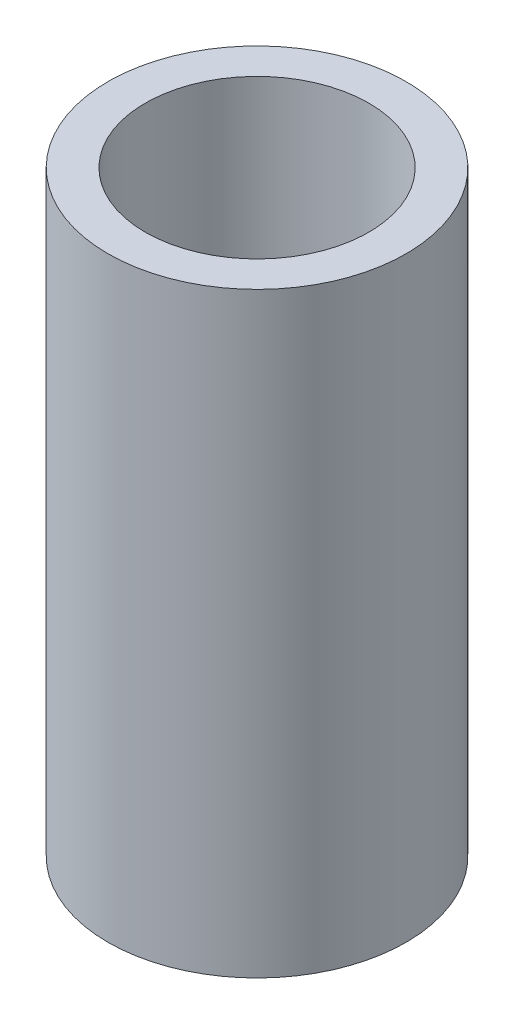
SolidWorks part; units mm, degrees
ref_plane "Front Plane" through (0, 0, 0) normal (0, 0, 1) x (1, 0, 0)
ref_plane "Top Plane" through (0, 0, 0) normal (0, 1, 0) x (1, 0, 0)
ref_plane "Right Plane" through (0, 0, 0) normal (1, 0, 0) x (0, 0, -1)
sketch "Sketch1" plane through (0, 0, 0) normal (0, 1, 0) x (1, 0, 0)
  circle A0 centre (0, 0) radius 1.5
  circle A1 centre (0, 0) radius 2
  dimension "D1" = 3
  dimension "D2" = 4
extrude "Boss-Extrude1" add sketch "Sketch1" along normal blind 8
